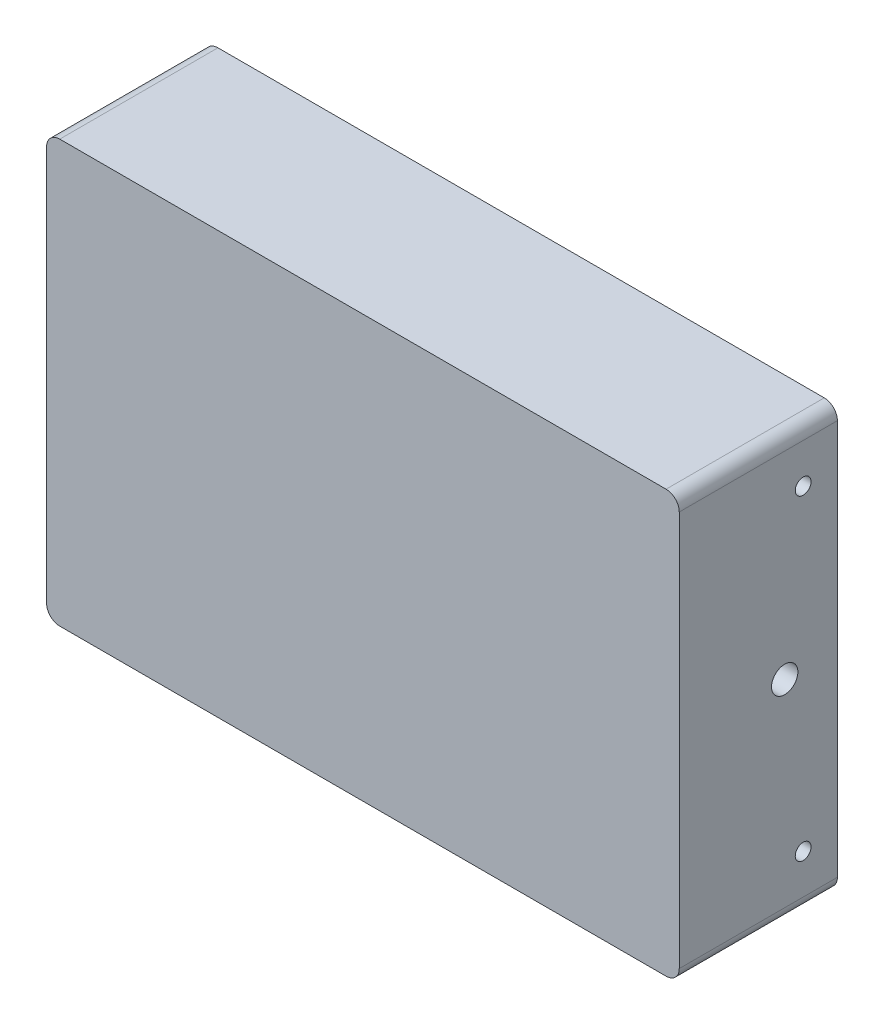
SolidWorks part; units mm, degrees
ref_plane "Front Plane" through (0, 0, 0) normal (0, 0, 1) x (1, 0, 0)
ref_plane "Top Plane" through (0, 0, 0) normal (0, 1, 0) x (1, 0, 0)
ref_plane "Right Plane" through (0, 0, 0) normal (1, 0, 0) x (0, 0, -1)
sketch "Sketch2" plane through (0, 0, 0) normal (0, 0, 1) x (1, 0, 0)
  line L1 (-37.5, 22.5) -> (37.5, 22.5)
  line L2 (-37.5, 22.5) -> (-37.5, -22.5)
  line L3 (-37.5, -22.5) -> (37.5, -22.5)
  line L4 (37.5, 22.5) -> (37.5, -22.5)
  line L5 (-37.5, 22.5) -> (37.5, -22.5) construction
  line L6 (-37.5, -22.5) -> (37.5, 22.5) construction
  line L7 (-37.5, 30) -> (37.5, 30)
  line L8 (-37.5, 30) -> (-37.5, -30)
  line L9 (-37.5, -30) -> (37.5, -30)
  line L10 (37.5, 30) -> (37.5, -30)
  line L11 (-37.5, 30) -> (37.5, -30) construction
  line L12 (-37.5, -30) -> (37.5, 30) construction
  line L18 (42.5, 22.5) -> (55, 22.5)
  line L19 (42.5, 22.5) -> (42.5, -22.5)
  line L20 (42.5, -22.5) -> (55, -22.5)
  line L21 (55, 22.5) -> (55, -22.5)
  line L22 (-55, 40) -> (55, 40)
  line L23 (-55, 40) -> (-55, -40)
  line L24 (-55, -40) -> (55, -40)
  line L25 (55, 40) -> (55, -40)
  line L26 (-55, 40) -> (55, -40) construction
  line L27 (-55, -40) -> (55, 40) construction
  circle A0 centre (-37.5, 30) radius 4
  circle A1 centre (37.5, 30) radius 4
  circle A2 centre (37.5, -30) radius 4
  circle A3 centre (-37.5, -30) radius 4
  point P0 (0, 0)
  point P5 (0, 0)
  point P23 (0, 0)
  point P28 (0, 0)
  dimension "D5" = 8
  dimension "D1" = 45
  dimension "D2" = 75
  dimension "D3" = 60
  dimension "D4" = 75
  dimension "D8" = 5
  dimension "D9" = 45
  dimension "D10" = 0
  dimension "D11" = 80
  dimension "D12" = 110
  dimension "D6" = 2
  dimension "D7" = 2
extrude "Boss-Extrude1" add sketch "Sketch2" along normal blind 20 contours L25 L22 L23 L24 L20 L19 L18 A3 L8 L2 A0 L7 A1 L10 L4 A2 L9 | A1 L7 A0 L8 L1 L10 | L4 L1 L2 L3 | A3 L9 A2 L10 L3 L8
sketch "Sketch3" plane through (0, 0, 20) normal (0, 0, 1) x (1, 0, 0)
  line L1 (-55, 40) -> (55, 40)
  line L2 (-55, 40) -> (-55, -40)
  line L3 (-55, -40) -> (55, -40)
  line L4 (55, 40) -> (55, -40)
  line L5 (-55, 40) -> (55, -40) construction
  line L6 (-55, -40) -> (55, 40) construction
  point P0 (0, 0)
  point P5 (0, 0)
  dimension "D1" = 110
  dimension "D2" = 80
extrude "Boss-Extrude2" add sketch "Sketch3" along normal blind 10
sketch "Sketch4" plane through (0, 0, 0) normal (0, 0, 1) x (1, 0, 0)
  line L1 (-45, 30) -> (45, 30)
  line L2 (-45, 30) -> (-45, -30)
  line L3 (-45, -30) -> (45, -30)
  line L4 (45, 30) -> (45, -30)
  line L5 (-45, 30) -> (45, -30) construction
  line L6 (-45, -30) -> (45, 30) construction
  line L7 (-46.25, 32.8) -> (-43.75, 32.8)
  line L8 (-46.25, 32.8) -> (-46.25, 27.2)
  line L9 (-46.25, 27.2) -> (-43.75, 27.2)
  line L10 (-43.75, 32.8) -> (-43.75, 27.2)
  line L11 (-46.25, 32.8) -> (-43.75, 27.2) construction
  line L12 (-46.25, 27.2) -> (-43.75, 32.8) construction
  line L20 (-46.25, -27.2) -> (-46.25, -32.8)
  line L21 (-46.25, -27.2) -> (-43.75, -27.2)
  line L22 (-43.75, -27.2) -> (-43.75, -32.8)
  line L23 (-46.25, -32.8) -> (-43.75, -32.8)
  line L32 (43.75, 32.8) -> (46.25, 32.8)
  line L33 (43.75, 32.8) -> (43.75, 27.2)
  line L34 (46.25, 32.8) -> (46.25, 27.2)
  line L35 (43.75, 27.2) -> (46.25, 27.2)
  line L36 (43.75, -27.2) -> (46.25, -27.2)
  line L37 (43.75, -27.2) -> (43.75, -32.8)
  line L38 (46.25, -27.2) -> (46.25, -32.8)
  line L39 (43.75, -32.8) -> (46.25, -32.8)
  line L40 (54.75, 32.8) -> (54.75, 27.2) [skipped]
  line L41 (54.75, 32.8) -> (57.25, 32.8) [skipped]
  line L42 (57.25, 32.8) -> (57.25, 27.2) [skipped]
  line L43 (54.75, 27.2) -> (57.25, 27.2) [skipped]
  line L44 (54.75, -27.2) -> (54.75, -32.8) [skipped]
  line L45 (54.75, -27.2) -> (57.25, -27.2) [skipped]
  line L46 (57.25, -27.2) -> (57.25, -32.8) [skipped]
  line L47 (54.75, -32.8) -> (57.25, -32.8) [skipped]
  point P0 (0, 0)
  point P5 (-45, 30)
  dimension "D1" = 2
  dimension "D2" = 5.6
  dimension "105" = 90
  dimension "D3" = 2.5
  dimension "D4" = 2
  dimension "D5" = 2
extrude "Cut-Extrude1" cut sketch "Sketch4" along normal blind 10 contours L4 L35 L34 L32 L33 L1 | L33 L35 L4 L1 | L10 L7 L8 L9 L2 L1 | L10 L1 L2 L9 | L22 L21 L2 L3 | L20 L23 L22 L3 L2 L21 | L37 L39 L38 L36 L4 L3 | L36 L37 L3 L4
sketch "Sketch5" plane through (55, 0, 0) normal (1, 0, 0) x (0, 0, -1)
  line L0 (0, 22.5) -> (0, -22.5) construction
  line L1 (-30, 40) -> (0, 40)
  line L2 (-30, 40) -> (-30, -40)
  line L3 (-30, -40) -> (0, -40)
  line L4 (0, 40) -> (0, -40)
  line L5 (-30, 40) -> (0, 40) construction
  dimension "D1" = 80
  dimension "D2" = 30
  dimension "D3" = 0
  dimension "D4" = 0
extrude "Boss-Extrude4" add sketch "Sketch5" along normal blind 10
sketch "Sketch8" plane through (65, 0, 0) normal (1, 0, 0) x (0, 0, -1)
  line L0 (0, -40) -> (0, 40) construction
  circle A0 centre (-6.5, 30) radius 1.5
  circle A1 centre (-6.5, -30) radius 1.5
  point P4 (0, 0)
  dimension "D1" = 3
  dimension "D2" = 3
  dimension "D3" = 60
  dimension "D4" = 30
  dimension "D5" = 6.5
extrude "Cut-Extrude2" cut sketch "Sketch8" against normal blind 120
sketch "Sketch9" plane through (42.5, 0, 0) normal (1, 0, 0) x (0, 0, -1)
  line L0 (-30, 40) -> (-30, -40) construction
  circle A0 centre (-10, 0) radius 2.5
  point P2 (0, 0)
  dimension "D1" = 5
  dimension "D2" = 20
extrude "Cut-Extrude3" cut sketch "Sketch9" against normal blind 20 and the other way blind 40
sketch "Sketch10" plane through (0, 0, 0) normal (0, 0, -1) x (-1, 0, 0)
  line L0 (-42.5, 22.5) -> (-42.5, -22.5) construction
  line L1 (-37.5, 4) -> (-33.8, 4)
  line L2 (-37.5, 4) -> (-37.5, -4)
  line L3 (-37.5, -4) -> (-33.8, -4)
  line L4 (-33.8, 4) -> (-33.8, -4)
  line L5 (-61.2, 4) -> (-57.5, 4)
  line L6 (-61.2, 4) -> (-61.2, -4)
  line L7 (-61.2, -4) -> (-57.5, -4)
  line L8 (-57.5, 4) -> (-57.5, -4)
  line L9 (-55, -22.5) -> (-55, 22.5) construction
  point P14 (-57.5, 0)
  point P15 (-37.5, 0)
  dimension "D1" = 8
  dimension "D2" = 3.7
  dimension "D3" = 5
  dimension "D4" = 8
  dimension "D5" = 3.7
  dimension "D6" = 2.5
extrude "Cut-Extrude4" cut sketch "Sketch10" against normal blind 15
fillet "Fillet1" radius 2.5 4 edges at (65, 40, 15) (65, -40, 15) (-55, -40, 15) (-55, 40, 15)
